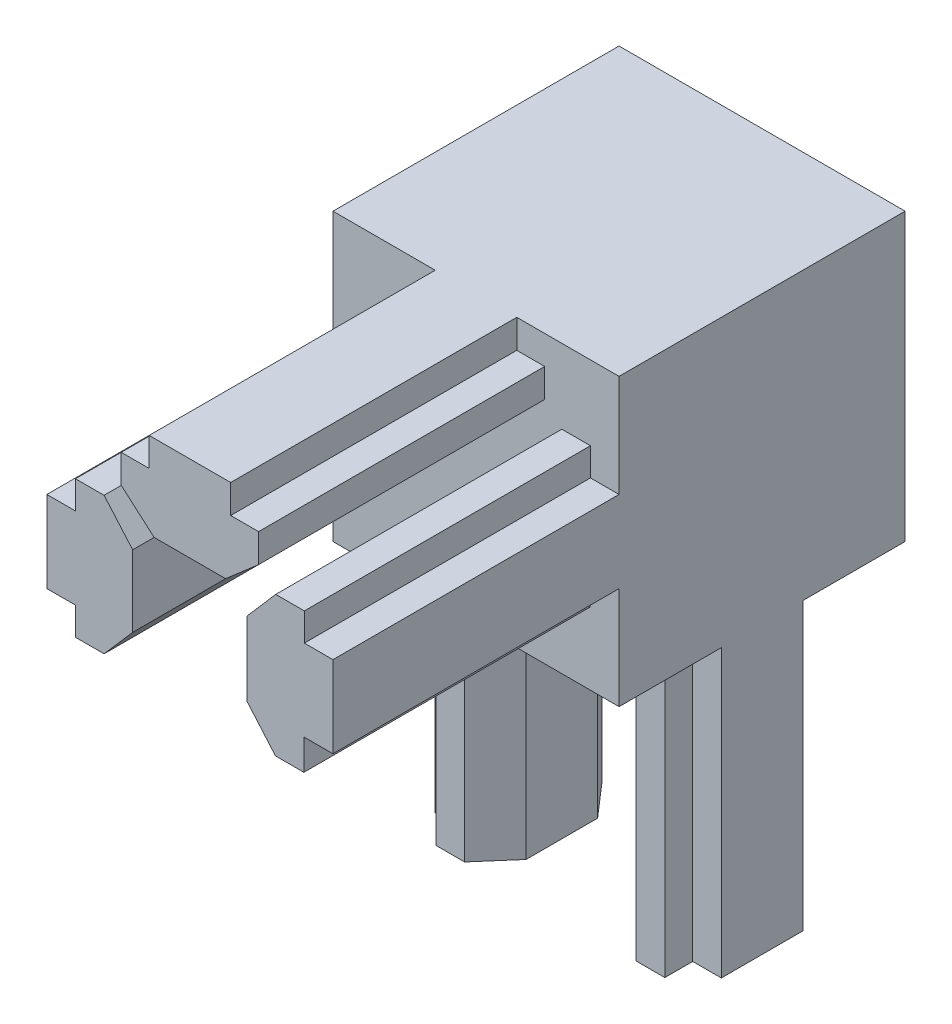
SolidWorks part; units mm, degrees
ref_plane "Front Plane" through (0, 0, 0) normal (0, 0, 1) x (1, 0, 0)
ref_plane "Top Plane" through (0, 0, 0) normal (0, 1, 0) x (1, 0, 0)
ref_plane "Right Plane" through (0, 0, 0) normal (1, 0, 0) x (0, 0, -1)
sketch "Sketch1" plane through (0, 0, 0) normal (0, 0, 1) x (1, 0, 0)
  line L1 (-10, -10) -> (10, -10)
  line L2 (-10, -10) -> (-10, 10)
  line L3 (-10, 10) -> (10, 10)
  line L4 (10, -10) -> (10, 10)
  line L5 (-10, -10) -> (10, 10) construction
  line L6 (-10, 10) -> (10, -10) construction
  point P0 (0, 0)
  dimension "D1" = 20
  dimension "D2" = 20
extrude "Boss-Extrude1" add sketch "Sketch1" along normal blind 20 contours L2 L1 L4 L3
sketch "Sketch2" plane through (0, 0, 20) normal (0, 0, 1) x (1, 0, 0)
  line L0 (2.85, 10) -> (2.85, 8)
  line L1 (-10, 10) -> (10, 10) construction
  line L2 (-2.85, 10) -> (-2.85, 8)
  line L3 (-2.85, 8) -> (-4.8, 8)
  line L4 (-4.8, 8) -> (-4.8, 6)
  line L5 (2.5, 4) -> (4.8, 6)
  line L6 (-2.85, 10) -> (2.85, 10)
  line L8 (4.8, 6) -> (4.8, 8)
  line L9 (4.8, 8) -> (2.85, 8)
  line L13 (-2.5, 4) -> (2.5, 4)
  line L14 (-4.8, 6) -> (-2.5, 4)
extrude "Boss-Extrude2" add sketch "Sketch2" along normal blind 20 contours L6 L0 L9 L8 L5 L13 L14 L4 L3 L2
sketch "Sketch3" plane through (0, 0, 20) normal (0, 0, 1) x (1, 0, 0)
  line L0 (-10, -10) -> (-10, 10) construction
  line L1 (-10, 2.85) -> (-8, 2.85)
  line L2 (-10, 2.85) -> (-10, -2.85)
  line L3 (-10, -2.85) -> (-8, -2.85)
  line L5 (-10, 10) -> (-2.85, 10) construction
  line L6 (-10, -10) -> (10, -10) construction
  line L7 (-8, 2.85) -> (-8, 4.8)
  line L12 (-8, -2.85) -> (-8, -4.8)
  line L15 (-4, -2.5) -> (-4, 2.5)
  line L16 (-6, 4.8) -> (-4, 2.5)
  line L17 (-6, -4.8) -> (-4, -2.5)
  line L18 (-8, 4.8) -> (-6, 4.8)
  line L19 (-8, -4.8) -> (-6, -4.8)
  dimension "D1" = 7.15
  dimension "D2" = 7.15
  dimension "D3" = 1.95
  dimension "D4" = 1.95
extrude "Boss-Extrude3" add sketch "Sketch3" along normal blind 20
sketch "Sketch4" plane through (0, 0, 20) normal (0, 0, 1) x (1, 0, 0)
  line L0 (10, -10) -> (10, 10) construction
  line L1 (10, 2.85) -> (8, 2.85)
  line L2 (10, 2.85) -> (10, -2.85)
  line L3 (10, -2.85) -> (7.9673, -2.85)
  line L7 (8, 4.8) -> (8, 2.85)
  line L12 (7.9673, -2.85) -> (7.9673, -4.9896)
  line L14 (4, 2.5) -> (4, -2.6896)
  line L16 (4, 2.5) -> (6, 4.8)
  line L17 (5.9837, -4.9896) -> (4, -2.6896)
  line L18 (5.9837, -4.9896) -> (7.9673, -4.9896)
  line L19 (6, 4.8) -> (8, 4.8)
extrude "Boss-Extrude4" add sketch "Sketch4" along normal blind 20
sketch "Sketch5" plane through (0, -10, 0) normal (0, -1, 0) x (1, 0, 0)
  line L0 (-10, 20) -> (-10, 0) construction
  line L1 (-10, 12.85) -> (-8, 12.85)
  line L2 (-10, 12.85) -> (-10, 7.15)
  line L3 (-10, 7.15) -> (-8, 7.15)
  line L5 (10, 20) -> (10, 0) construction
  line L6 (10, 12.85) -> (8, 12.85)
  line L7 (10, 12.85) -> (10, 7.15)
  line L8 (10, 7.15) -> (8, 7.15)
  line L10 (-10, 0) -> (10, 0) construction
  line L11 (-2.85, 0) -> (2.85, 0)
  line L12 (-2.85, 0) -> (-2.85, 2)
  line L14 (2.85, 0) -> (2.85, 2)
  line L16 (-4, 12.5) -> (-4, 7.5)
  line L30 (-8, 14.8) -> (-8, 12.85)
  line L31 (-8, 7.15) -> (-8, 5.2)
  line L32 (-6, 14.8) -> (-4, 12.5)
  line L33 (-4, 7.5) -> (-6, 5.2)
  line L34 (-8, 14.8) -> (-6, 14.8)
  line L35 (-8, 5.2) -> (-6, 5.2)
  line L37 (-2.5, 6) -> (2.5, 6)
  line L39 (-4.8, 2) -> (-2.85, 2)
  line L40 (2.85, 2) -> (4.8, 2)
  line L41 (-4.8, 4) -> (-2.5, 6)
  line L42 (2.5, 6) -> (4.8, 4)
  line L43 (-4.8, 4) -> (-4.8, 2)
  line L44 (4.8, 4) -> (4.8, 2)
  line L45 (8, 14.8) -> (8, 12.85)
  line L46 (8, 7.15) -> (8, 5.2)
  line L49 (4, 12.5) -> (4, 7.5)
  line L51 (4, 12.5) -> (6, 14.8)
  line L53 (6, 5.2) -> (4, 7.5)
  line L54 (6, 14.8) -> (8, 14.8)
  line L55 (6, 5.2) -> (8, 5.2)
  dimension "D5" = 5
extrude "Boss-Extrude5" add sketch "Sketch5" along normal blind 20
